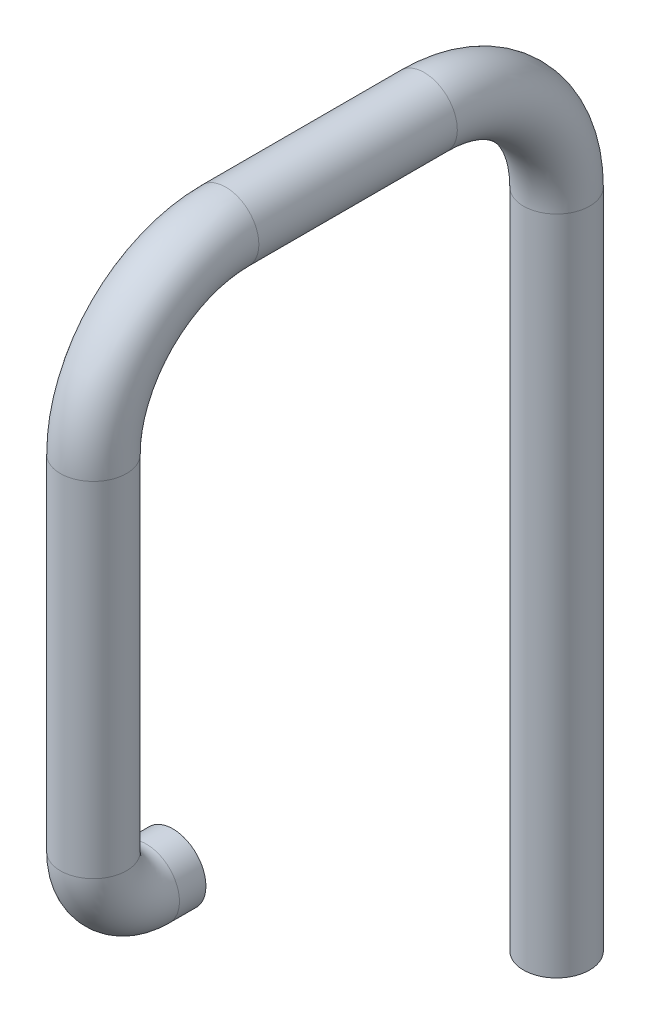
SolidWorks part; units mm, degrees
ref_plane "Front Plane" through (0, 0, 0) normal (0, 0, 1) x (1, 0, 0)
ref_plane "Top Plane" through (0, 0, 0) normal (0, 1, 0) x (1, 0, 0)
ref_plane "Right Plane" through (0, 0, 0) normal (1, 0, 0) x (0, 0, -1)
sketch "Sketch1" plane through (0, 0, 0) normal (1, 0, 0) x (0, 0, -1)
  line L0 (0, 0) -> (-2, 0)
  line L1 (-6, 4) -> (-6, 30)
  line L2 (4, 40) -> (19, 40)
  line L3 (29, 30) -> (29, -20)
  arc A0 (19, 40) -> (29, 30) centre (19, 30) cw
  arc A1 (-6, 30) -> (4, 40) centre (4, 30) cw
  arc A2 (-2, 0) -> (-6, 4) centre (-2, 4) cw
  point P8 (29, 40)
  point P11 (-6, 40)
  point P14 (-6, 0)
  dimension "D5" = 10
  dimension "D6" = 4
  dimension "D1" = 6
  dimension "D2" = 40
  dimension "D3" = 35
  dimension "D4" = 60
sketch "Sketch2" plane through (0, 0, 0) normal (0, 0, 1) x (1, 0, 0)
  circle A0 centre (0, 0) radius 2.5
  dimension "D1" = 5
sweep "Sweep1" add profiles "Sketch2" path "Sketch1"
